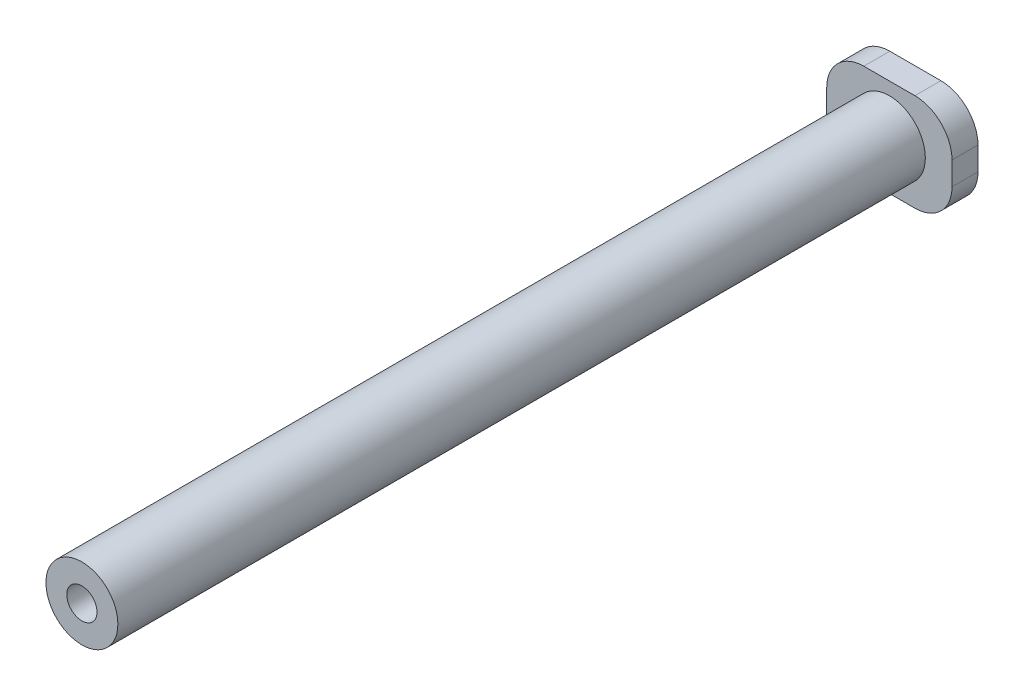
SolidWorks part; units mm, degrees
ref_plane "Front Plane" through (0, 0, 0) normal (0, 0, 1) x (1, 0, 0)
ref_plane "Top Plane" through (0, 0, 0) normal (0, 1, 0) x (1, 0, 0)
ref_plane "Right Plane" through (0, 0, 0) normal (1, 0, 0) x (0, 0, -1)
sketch "Sketch4" plane through (0, 0, 0) normal (0, 0, 1) x (1, 0, 0)
  line L1 (0, 0) -> (13.5, 0)
  line L2 (0, 0) -> (0, 10.5)
  line L3 (0, 10.5) -> (13.5, 10.5)
  line L4 (13.5, 0) -> (13.5, 10.5)
  dimension "D1" = 10.5
  dimension "D2" = 13.5
extrude "Boss-Extrude2" add sketch "Sketch4" along normal blind 2.8
sketch "Sketch5" plane through (0, 0, 2.8) normal (0, 0, 1) x (1, 0, 0)
  line L0 (0, 0) -> (13.5, 0) construction
  line L2 (13.5, 0) -> (13.5, 10.5) construction
  circle A0 centre (6.75, 5.25) radius 3.875
  dimension "D1" = 7.75
  dimension "D2" = 5.25
  dimension "D3" = 6.75
extrude "Boss-Extrude3" add sketch "Sketch5" along normal blind 87
sketch "Sketch6" plane through (0, 0, 89.8) normal (0, 0, 1) x (1, 0, 0)
  circle A0 centre (6.75, 5.25) radius 1.63
extrude "Cut-Extrude1" cut sketch "Sketch6" against normal through all
fillet "Fillet1" radius 4 4 edges at (13.5, 0, 1.4) (0, 0, 1.4) (0, 10.5, 1.4) (13.5, 10.5, 1.4)
ref_plane "Front" through (0, 0, 44.9) normal (0, 0, -1) x (-1, 0, 0)
ref_plane "Top" through (0, 5.25, 0) normal (0, 1, 0) x (1, 0, 0)
ref_plane "Right" through (6.75, 0, 0) normal (1, 0, 0) x (0, 0, -1)
